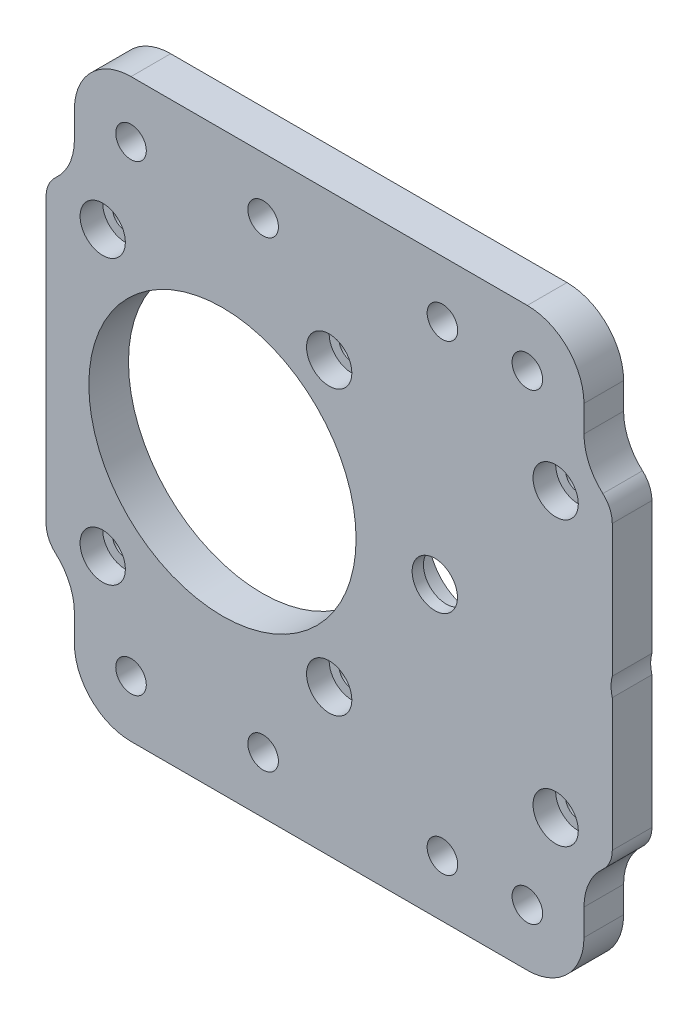
SolidWorks part; units mm, degrees
ref_plane "Front Plane" through (0, 0, 0) normal (0, 0, 1) x (1, 0, 0)
ref_plane "Top Plane" through (0, 0, 0) normal (0, 1, 0) x (1, 0, 0)
ref_plane "Right Plane" through (0, 0, 0) normal (1, 0, 0) x (0, 0, -1)
sketch "Sketch2" plane through (0, 0, -75.5263) normal (0, 0, 1) x (1, 0, 0)
  line L0 (-21.15, 25) -> (18.85, 25) construction
  line L1 (18.85, 25) -> (58.85, 25) construction
  line L2 (-21.15, -25) -> (18.85, -25) construction
  line L3 (18.85, -25) -> (58.85, -25) construction
  line L8 (63.85, 30) -> (-26.15, 30)
  line L9 (-31.15, 25) -> (-31.15, -25)
  line L10 (-26.15, -30) -> (63.85, -30)
  line L11 (68.85, -25) -> (68.85, 25)
  arc A8 (-26.15, 30) -> (-31.15, 25) centre (-26.15, 25) ccw
  arc A9 (-31.15, -25) -> (-26.15, -30) centre (-26.15, -25) ccw
  arc A10 (63.85, -30) -> (68.85, -25) centre (63.85, -25) ccw
  arc A11 (68.85, 25) -> (63.85, 30) centre (63.85, 25) ccw
  circle A14 centre (58.85, 25) radius 2.15
  circle A15 centre (18.85, 25) radius 2.15
  circle A16 centre (-21.15, 25) radius 2.15
  circle A17 centre (-21.15, -25) radius 2.15
  circle A18 centre (18.85, -25) radius 2.15
  circle A19 centre (58.85, -25) radius 2.15
  circle A20 centre (0, 0) radius 23.6
  dimension "D2" = 47.2
  dimension "D10" = 5
  dimension "D1" = 31.15
  dimension "D3" = 30
  dimension "D4" = 100
  dimension "D5" = 60
  dimension "D6" = 40
  dimension "D7" = 40
  dimension "D8" = 5
  dimension "D9" = 50
  dimension "D11" = 40
  dimension "D12" = 40
  dimension "D13" = 5
  dimension "D14" = 50
extrude "Boss-Extrude1" add sketch "Sketch2" along normal blind 7
sketch "Sketch3" plane through (0, 0, -68.5263) normal (0, 0, 1) x (1, 0, 0)
  line L0 (0, 0) -> (23.6, 0) construction
  line L1 (23.6, 0) -> (51.4, 0) construction
  circle A0 centre (37.5, 0) radius 8.1
  circle A1 centre (0, 0) radius 23.6
  dimension "D1" = 16.2
  dimension "D2" = 47.2
  dimension "D3" = 23.6
  dimension "D4" = 37.5
extrude "Cut-Extrude1" cut sketch "Sketch3" along normal blind 5 from surface at -7 starting at face at (18.85, 0, -75.5263)
sketch "Sketch4" plane through (0, 0, -70.5263) normal (0, 0, -1) x (-1, 0, 0)
  circle A0 centre (-37.5, 0) radius 4
  circle A1 centre (-37.5, 0) radius 8.1 construction
  dimension "D1" = 8
extrude "Cut-Extrude2" cut sketch "Sketch4" against normal blind 5
sketch "Sketch5" plane through (0, 0, -68.5263) normal (0, 0, 1) x (1, 0, 0)
  line L0 (0, 0) -> (37.5, 0) construction
  line L1 (37.5, 0) -> (75, 0) construction
  circle A0 centre (0, 0) radius 25 construction
  circle A1 centre (37.5, 0) radius 12.5 construction
  circle A2 centre (75, 0) radius 25 construction
  circle A3 centre (75, 0) radius 6.365
  dimension "D1" = 50
  dimension "D2" = 25
  dimension "D5" = 50
  dimension "D6" = 12.73
  dimension "D3" = 37.5
  dimension "D4" = 37.5
extrude "Cut-Extrude3" cut sketch "Sketch5" against normal blind 10
sketch "Sketch6" plane through (0, 0, -75.5263) normal (0, 0, -1) x (-1, 0, 0)
  line L0 (-68.85, 25) -> (-68.85, 1.6403)
  line L1 (-68.85, -1.6403) -> (-68.85, -25)
  arc A0 (-68.85, 25) -> (-68.85, -25) centre (-68.85, 0) ccw
  circle A1 centre (-75, 0) radius 6.365 construction
  circle A2 centre (-75, 0) radius 6.365
  line M5 (-68.85, 25) -> (-68.85, 1.6403)
  line M7 (-68.85, -1.6403) -> (-68.85, -25)
  dimension "D1" = 50
  dimension "D2" = 50
  dimension "D3" = 25
extrude "Boss-Extrude2" [suppressed] add sketch "Sketch6" against normal blind 7 contours A2 A0 M5 M7
fillet "Fillet1" [suppressed] radius 10
hole_wizard "CBORE for M4 SHCS1" positions "3DSketch1" profile "Sketch7" counterbore size "M4" standard "ANSI Metric" end condition through all
sketch3d "3DSketch1"
  line L0 (-21.15, 25, -68.5263) -> (-21.15, 25, -75.5263) construction
  line L1 (18.85, 25, -68.5263) -> (18.85, 25, -75.5263) construction
  line L2 (58.85, 25, -68.5263) -> (58.85, 25, -75.5263) construction
  line L3 (58.85, -25, -68.5263) -> (58.85, -25, -75.5263) construction
  line L4 (18.85, -25, -68.5263) -> (18.85, -25, -75.5263) construction
  line L5 (-21.15, -25, -68.5263) -> (-21.15, -25, -75.5263) construction
  point P0 (-21.15, 25, -68.5263)
  point P4 (18.85, 25, -68.5263)
  point P8 (58.85, 25, -68.5263)
  point P12 (58.85, -25, -68.5263)
  point P16 (18.85, -25, -68.5263)
  point P20 (-21.15, -25, -68.5263)
sketch "Sketch7" plane through (-21.15, 25, -68.5263) normal (1, 0, 0) x (0, -1, 0)
  line L0 (0, 0) -> (0, 7)
  line L1 (0, 7) -> (2.25, 7)
  line L3 (2.25, 7) -> (2.25, 4)
  line L4 (2.25, 4) -> (4, 4)
  line L5 (4, 4) -> (4, 0)
  line L7 (4, 0) -> (0, 0)
  line L11 (0, -6.35) -> (0, 107.95) construction
  dimension "Thru Hole Dia." = 4.5
  dimension "Thru Hole Depth" = 7
  dimension "C'Bore Dia." = 8
  dimension "C'Bore Depth" = 4
sketch "Sketch9" plane through (0, 0, -68.5263) normal (0, 0, 1) x (1, 0, 0)
  line L0 (-26.15, 30) -> (-26.15, 50.85)
  line L1 (63.85, 30) -> (63.85, 50.85)
  line L2 (63.85, 30) -> (-26.15, 30) construction
  line L3 (63.85, 50.85) -> (-26.15, 50.85)
  line L4 (63.85, 30) -> (-26.15, 30)
  line L5 (0, 0) -> (-31.15, 0) construction
  line L7 (-31.15, 25) -> (-31.15, -25) construction
  line L8 (-26.15, 40.85) -> (63.85, 40.85) construction
  line L9 (63.85, -30) -> (63.85, -50.85)
  line L10 (63.85, -50.85) -> (-26.15, -50.85)
  line L11 (-26.15, -30) -> (-26.15, -50.85)
  line L12 (63.85, -30) -> (-26.15, -30)
  circle A1 centre (-16.15, 40.85) radius 2.7
  circle A2 centre (7.1833, 40.85) radius 2.7
  circle A4 centre (53.85, 40.85) radius 2.7
  circle A5 centre (53.85, -40.85) radius 2.7
  circle A7 centre (7.1833, -40.85) radius 2.7
  circle A8 centre (-16.15, -40.85) radius 2.7
  circle A9 centre (30.5167, 40.85) radius 2.7 [skipped]
  circle A10 centre (38.85, 40.85) radius 2.7
  circle A11 centre (38.85, -40.85) radius 2.7
  dimension "D7" = 5.4
  dimension "D11" = 5.4
  dimension "D12" = 5.4
  dimension "D13" = 15
  dimension "D1" = 20.85
  dimension "D2" = 20.85
  dimension "D3" = 90
  dimension "D4" = 31.15
  dimension "D5" = 90
  dimension "D6" = 10
  dimension "D8" = 10
  dimension "D10" = 10
  dimension "D9" = 4
extrude "Boss-Extrude3" add sketch "Sketch9" against normal up to surface (7 mm away) up to face at (-18.9, 25, -75.5263)
fillet "Fillet2" radius 10 8 edges at (63.85, 30, -72.0263) (63.85, 50.85, -72.0263) (-26.15, 50.85, -72.0263) (-26.15, 30, -72.0263) (-26.15, -30, -72.0263) (63.85, -50.85, -72.0263) (63.85, -30, -72.0263) (-26.15, -50.85, -72.0263)
sketch "Sketch10" plane through (0, 0, -68.5263) normal (0, 0, 1) x (1, 0, 0)
  line L1 (-27.5, 50.85) -> (27.5, 50.85)
  line L2 (-27.5, 50.85) -> (-27.5, -50.85)
  line L3 (-27.5, -50.85) -> (27.5, -50.85)
  line L4 (27.5, 50.85) -> (27.5, -50.85)
  line L5 (-27.5, 50.85) -> (27.5, -50.85) construction
  line L6 (-27.5, -50.85) -> (27.5, 50.85) construction
  line L7 (-16.15, -50.85) -> (53.85, -50.85) construction
  circle A0 centre (0, 0) radius 23.6 construction
  circle A1 centre (0, 0) radius 23.6
  circle A2 centre (-21.15, 25) radius 2.25
  circle A3 centre (18.85, 25) radius 2.25
  circle A4 centre (18.85, -25) radius 2.25
  circle A5 centre (-21.15, -25) radius 2.25
  circle A6 centre (-16.15, -40.85) radius 2.7 construction
  circle A7 centre (7.1833, -40.85) radius 2.7 construction
  circle A8 centre (7.1833, 40.85) radius 2.7 construction
  circle A9 centre (-16.15, 40.85) radius 2.7 construction
  circle A10 centre (-16.15, -40.85) radius 2.7
  circle A11 centre (7.1833, -40.85) radius 2.7
  circle A12 centre (7.1833, 40.85) radius 2.7
  circle A13 centre (-16.15, 40.85) radius 2.7
  circle A14 centre (-21.15, 25) radius 2.25 construction
  circle A15 centre (18.85, 25) radius 2.25 construction
  circle A16 centre (-21.15, -25) radius 2.25 construction
  circle A17 centre (18.85, -25) radius 2.25 construction
  dimension "D1" = 4.5
  dimension "D2" = 4.5
  dimension "D3" = 4.5
  dimension "D4" = 4.5
  dimension "D5" = 101.7
  dimension "D6" = 55
extrude "Boss-Extrude4" add sketch "Sketch10" along normal blind 7 separate body
delete or keep bodies "Body-Delete/Keep 1" type delete bodies bodies 108
sketch "Sketch13" [suppressed] plane through (0, 0, -68.5263) normal (0, 0, 1) x (1, 0, 0)
  circle A0 centre (75, 0) radius 6.365 construction
  circle A1 centre (75, 0) radius 6.365
  circle A2 centre (75, 0) radius 5
  dimension "D1" = 10
extrude "Boss-Extrude5" [suppressed] add sketch "Sketch13" against normal blind 3
sketch "Sketch14" plane through (0, 0, -68.5263) normal (0, 0, 1) x (1, 0, 0)
  circle A0 centre (0, 0) radius 23.6
  circle A1 centre (0, 0) radius 22
  dimension "D1" = 47.2
  dimension "D2" = 44
extrude "Boss-Extrude6" [suppressed] add sketch "Sketch14" against normal blind 2
